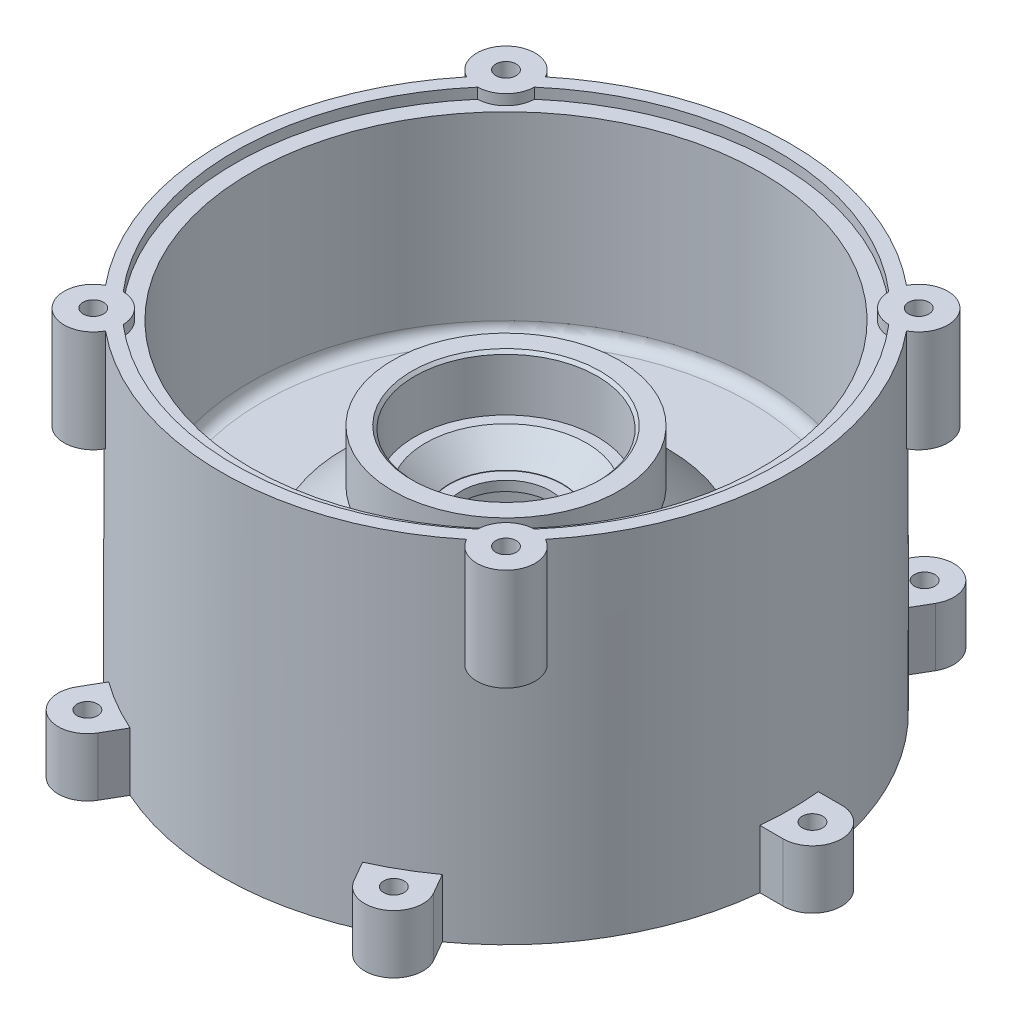
SolidWorks part; units mm, degrees
ref_plane "Plano frontal" through (0, 0, 0) normal (0, 0, 1) x (1, 0, 0)
ref_plane "Plano superior" through (0, 0, 0) normal (0, 1, 0) x (1, 0, 0)
ref_plane "Plano direito" through (0, 0, 0) normal (1, 0, 0) x (0, 0, -1)
sketch "Esboço3" plane through (0, 0, 0) normal (0, 0, 1) x (1, 0, 0)
  line L2 (97.5, 120) -> (97.5, 11.3045)
  line L4 (82.8424, 0) -> (60.3424, 0)
  line L5 (31.3, 66.16) -> (27.6265, 66.16)
  line L6 (60.3424, 0) -> (60.3424, 40)
  line L7 (60.3424, 40) -> (52, 40)
  line L8 (52, 40) -> (44, 48)
  line L9 (44, 48) -> (31, 48)
  line L10 (31, 48) -> (31, 50.75)
  line L11 (31, 50.75) -> (22.6, 50.75)
  line L12 (22.6, 50.75) -> (22.6, 54.05)
  line L13 (22.6, 54.05) -> (19.3, 54.05)
  line L14 (19.3, 54.05) -> (19.3, 54.75)
  line L15 (19.3, 54.75) -> (15.3, 54.75)
  line L16 (15.3, 54.75) -> (15.3, 58.1)
  line L17 (15.3, 58.1) -> (19.3, 58.1)
  line L18 (97.5, 120) -> (93, 120)
  line L19 (93, 120) -> (93, 116.4)
  line L20 (93, 116.4) -> (87.5, 116.4)
  line L21 (87.5, 116.4) -> (87.5, 54.4)
  line L22 (83.5, 50.4) -> (55.5, 50.4)
  line L23 (55.5, 50.4) -> (38.8, 67.1)
  line L24 (38.8, 67.1) -> (38.8, 85.16)
  line L25 (38.8, 85.16) -> (32.3, 85.16)
  line L26 (32.3, 85.16) -> (31.3, 84.16)
  line L27 (31.3, 84.16) -> (31.3, 66.16)
  line L29 (19.3, 58.1) -> (19.3, 58.25)
  line L30 (55, 0) -> (-55, 0) construction
  line L31 (27.6265, 66.16) -> (19.3, 58.25)
  line L32 (82.8424, 0) -> (97.5, 0)
  line L33 (97.5, 0) -> (97.5, 11.3045)
  arc A1 (87.5, 54.4) -> (83.5, 50.4) centre (83.5, 54.4) cw
  dimension "D32" = 120
  dimension "D2" = 7.5
  dimension "D3" = 135
  dimension "D4" = 19
  dimension "D5" = 40
  dimension "D6" = 0.15
  dimension "D7" = 135
  dimension "D8" = 16
  dimension "D9" = 34.84
  dimension "D10" = 28
  dimension "D11" = 66
  dimension "D12" = 3.6
  dimension "D13" = 93
  dimension "D14" = 10
  dimension "D16" = 1
  dimension "D17" = 31.3
  dimension "D19" = 52
  dimension "D20" = 44
  dimension "D21" = 135
  dimension "D22" = 31
  dimension "D23" = 22.6
  dimension "D24" = 19.3
  dimension "D25" = 15.3
  dimension "D26" = 2.75
  dimension "D27" = 3.3
  dimension "D28" = 0.7
  dimension "D29" = 3.35
  dimension "D31" = 97.5
ref_axis "Eixo1" through (0, -3.6312, 0) along (0, 1, 0)
revolve "Revolução2" add sketch "Esboço3" angle 360 about axis through (0, -3.6312, 0) along (0, 1, 0)
sketch "Esboço4" plane through (0, 120, 0) normal (0, 1, 0) x (1, 0, 0)
  line L0 (70.71, 70.71) -> (-70.71, 70.71) construction
  line L1 (-70.71, 70.71) -> (-70.71, -70.71) construction
  line L2 (-70.71, -70.71) -> (70.71, -70.71) construction
  line L3 (70.71, -70.71) -> (70.71, 70.71) construction
  line L4 (-55, 0) -> (55, 0) construction
  line L5 (0, -55) -> (0, 55) construction
  circle A0 centre (70.71, 70.71) radius 10
  circle A1 centre (70.71, -70.71) radius 10
  circle A2 centre (-70.71, -70.71) radius 10
  circle A3 centre (-70.71, 70.71) radius 10
  point P0 (70.71, 0)
  point P8 (0, -70.71)
  dimension "D2" = 20
  dimension "D1" = 141.42
extrude "Ressalto-extrusão1" add sketch "Esboço4" against normal blind 35
sketch "Esboço5" plane through (0, 0, 0) normal (0, -1, 0) x (1, 0, 0)
  line L1 (0, 0) -> (-105, 0) construction
  line L2 (-105, -10) -> (-96.9858, -10)
  line L3 (-105, 10) -> (-96.9858, 10)
  line L4 (-96.9858, -10) -> (-96.9858, 10)
  arc A1 (-105, -10) -> (-105, 10) centre (-105, 0) cw
  circle A2 centre (0, 0) radius 97.5 construction
  point P1 (-10, -96.9858)
  point P5 (-105.3449, 4.7504)
  dimension "D2" = 10
  dimension "D1" = 105
extrude "Ressalto-extrusão2" add sketch "Esboço5" against normal blind 20
sketch "Esboço8" plane through (0, 0, 0) normal (0, -1, 0) x (1, 0, 0)
  circle A0 centre (-105, 0) radius 3.5
  dimension "D1" = 7
extrude "Corte-extrusão2" cut sketch "Esboço8" against normal blind 20
pattern_circular "PadrãoCircular1" count 6 over 360 about axis through (0, 0, 0) along (0, 1, 0) of "Ressalto-extrusão2", "Corte-extrusão2"
sketch "Esboço6" plane through (0, 120, 0) normal (0, 1, 0) x (1, 0, 0)
  circle A0 centre (-70.71, -70.71) radius 3.5
  circle A1 centre (70.71, -70.71) radius 3.5
  circle A2 centre (70.71, 70.71) radius 3.5
  circle A3 centre (-70.71, 70.71) radius 3.5
  dimension "D1" = 7
extrude "Corte-extrusão1" cut sketch "Esboço6" against normal blind 15
sketch "Esboço9" plane through (0, 50.75, 0) normal (0, -1, 0) x (1, 0, 0)
  line L0 (0, 0) -> (0, 26.5) construction
  circle A0 centre (0, 26.5) radius 1.25
  circle A1 centre (26.5, 0) radius 1.25
  circle A2 centre (0, -26.5) radius 1.25
  circle A3 centre (-26.5, 0) radius 1.25
  point P13 (0, 0)
  dimension "D2" = 2.5
  dimension "D1" = 26.5
  dimension "D3" = 4
extrude "Corte-extrusão3" cut sketch "Esboço9" against normal blind 6
